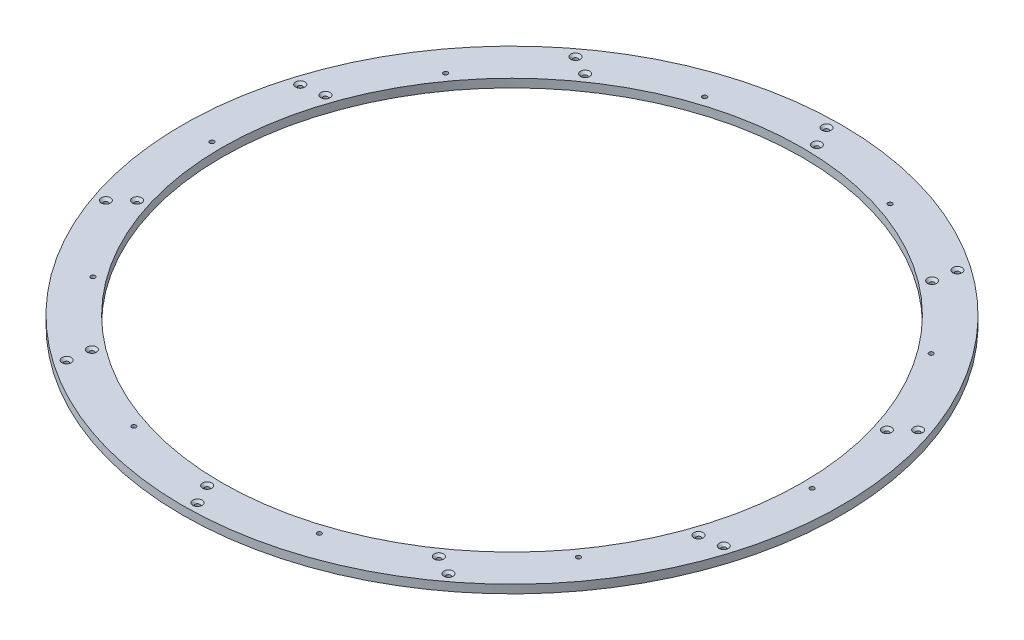
SolidWorks part; units mm, degrees
ref_plane "Front Plane" through (0, 0, 0) normal (0, 0, 1) x (1, 0, 0)
ref_plane "Top Plane" through (0, 0, 0) normal (0, 1, 0) x (1, 0, 0)
ref_plane "Right Plane" through (0, 0, 0) normal (1, 0, 0) x (0, 0, -1)
sketch "Sketch1" plane through (0, 0, 0) normal (0, 1, 0) x (1, 0, 0)
  circle A0 centre (0, 0) radius 295
  circle A1 centre (0, 0) radius 335
  dimension "D1" = 590
  dimension "D2" = 670
extrude "Boss-Extrude1" add sketch "Sketch1" along normal blind 8.5
hole_wizard "CBORE for M4 SHCS1" positions "Sketch2" profile "Sketch3" counterbore size "M4" standard "ANSI Metric" end condition through all
sketch "Sketch2" plane through (-255.5971, 32.5, 6.3126) normal (0, 1, 0) x (-0.9223, 0, -0.3865)
  point P3 (-208.1215, -408.5616)
  point P9 (-34.2671, -335.712)
  point P15 (63.5641, -174.5865)
  point P21 (48.004, 13.2706)
  point P27 (-75.004, 156.1041)
  point P33 (-258.475, 199.3566)
  point P39 (-432.3293, 126.507)
  point P45 (-530.1606, -34.6185)
  point P51 (-514.6005, -222.4755)
  point P57 (-391.5925, -365.3091)
sketch "Sketch3" plane through (94.2502, 32.5, -290.0722) normal (1, 0, 0) x (0, 0, 1)
  line L0 (0, 0) -> (0, 32.5)
  line L1 (0, 32.5) -> (2.25, 32.5)
  line L2 (2.25, 32.5) -> (2.25, 4)
  line L3 (2.25, 4) -> (4, 4)
  line L4 (4, 4) -> (4, 0)
  line L5 (4, 0) -> (0, 0)
  line L6 (0, -6.35) -> (0, 107.95) construction
  dimension "Thru Hole Dia." = 4.5
  dimension "Thru Hole Depth" = 32.5
  dimension "C'Bore Dia." = 8
  dimension "C'Bore Depth" = 4
hole_wizard "CSK for M4 Flat Head Machine Screw1" positions "Sketch4" profile "Sketch5" countersink size "M4" standard "ANSI Metric" end condition through all
sketch "Sketch4" plane through (68.2923, 8.5, -24.8286) normal (0, 1, 0) x (1, 0, 0)
  point P0 (-375.7267, -130.2282)
  point P3 (-378.9643, 70.6068)
  point P6 (-263.5358, 234.9887)
  point P9 (-73.5308, 300.1292)
  point P12 (118.475, 241.1469)
  point P15 (239.1421, 80.5711)
  point P18 (242.3797, -120.2639)
  point P21 (126.9511, -284.6458)
  point P24 (-63.0538, -349.7863)
  point P27 (-255.0596, -290.804)
  point P31 (-359.846, -114.3909)
  point P34 (-356.8077, 74.0849)
  point P37 (-243.5663, 224.7792)
  point P40 (-63.3762, 280.1318)
  point P43 (114.9362, 218.9999)
  point P46 (223.2614, 64.7338)
  point P49 (220.2231, -123.742)
  point P52 (106.9816, -274.4363)
  point P55 (-73.2085, -329.7889)
  point P58 (-251.5208, -268.657)
sketch "Sketch5" plane through (-307.4344, 8.5, 105.3996) normal (1, 0, 0) x (0, 0, 1)
  line L0 (0, 0) -> (0, 8.5)
  line L1 (0, 8.5) -> (2.25, 8.5)
  line L2 (2.25, 8.5) -> (2.25, 2.45)
  line L3 (2.25, 2.45) -> (4.7, 0)
  line L4 (4.7, 0) -> (0, 0)
  line L5 (-2.25, 2.45) -> (-4.7, 0) construction
  line L6 (0, -6.35) -> (0, 107.95) construction
  dimension "Thru Hole Dia." = 4.5
  dimension "Thru Hole Depth" = 8.5
  dimension "Near C'Sink Dia." = 9.4
  dimension "Near C'Sink Angle" = 90
